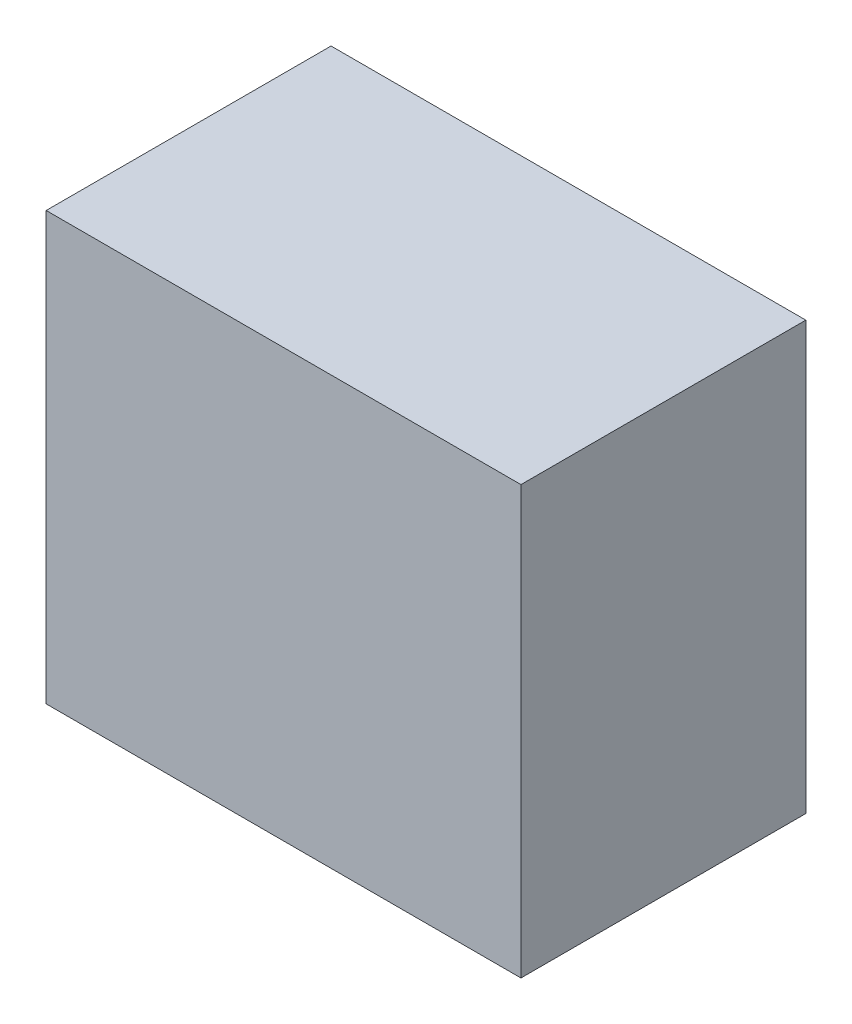
SolidWorks part; units mm, degrees
ref_plane "Front Plane" through (0, 0, 0) normal (0, 0, 1) x (1, 0, 0)
ref_plane "Top Plane" through (0, 0, 0) normal (0, 1, 0) x (1, 0, 0)
ref_plane "Right Plane" through (0, 0, 0) normal (1, 0, 0) x (0, 0, -1)
sketch "Sketch1" plane through (0, 0, 0) normal (0, 0, 1) x (1, 0, 0)
  line L1 (-508, 457.2) -> (508, 457.2)
  line L2 (-508, 457.2) -> (-508, -457.2)
  line L3 (-508, -457.2) -> (508, -457.2)
  line L4 (508, 457.2) -> (508, -457.2)
  line L5 (-508, 457.2) -> (508, -457.2) construction
  line L6 (-508, -457.2) -> (508, 457.2) construction
  point P0 (0, 0)
  dimension "D1" = 914.4
  dimension "D2" = 1016
extrude "Boss-Extrude1" add sketch "Sketch1" along normal blind 609.6
